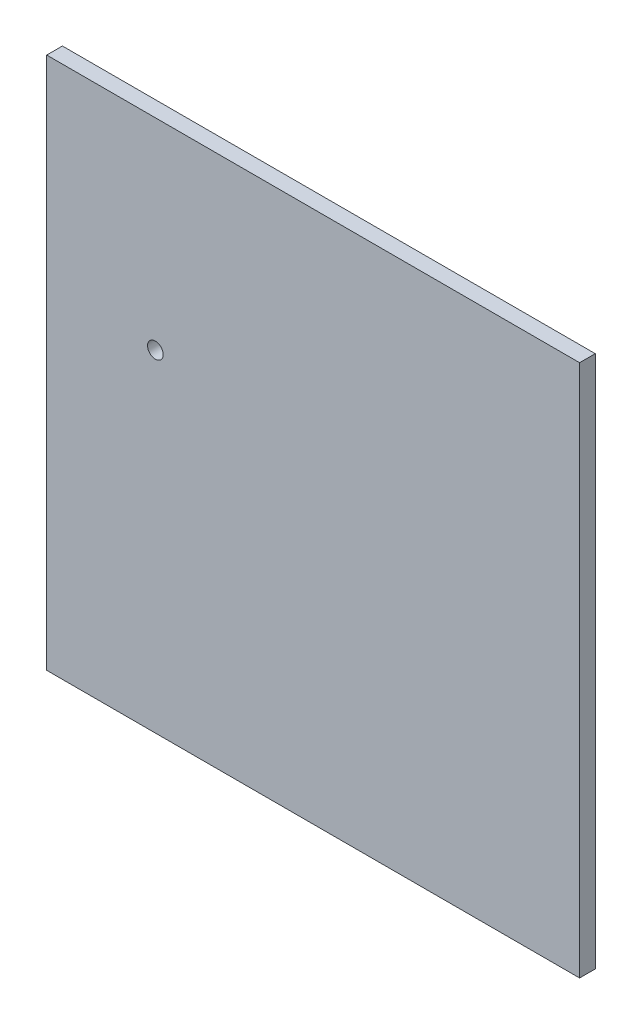
SolidWorks part; units mm, degrees
ref_plane "Plan de face" through (0, 0, 0) normal (1, 0, 0) x (0, 1, 0)
ref_plane "Plan de dessus" through (0, 0, 0) normal (0, 0, 1) x (0, 1, 0)
ref_plane "Plan de droite" through (0, 0, 0) normal (0, 1, 0) x (-1, 0, 0)
sketch "Esquisse3" plane through (0, 0, 0) normal (0, 0, 1) x (0, 1, 0)
  line L1 (-17, -17) -> (17, -17)
  line L2 (-17, -17) -> (-17, 17)
  line L3 (-17, 17) -> (17, 17)
  line L4 (17, -17) -> (17, 17)
  line L5 (-17, -17) -> (17, 17) construction
  line L6 (-17, 17) -> (17, -17) construction
  point P0 (0, 0)
  dimension "D1" = 34
  dimension "D2" = 34
extrude "Boss.-Extru.1" add sketch "Esquisse3" along normal blind 1
sketch "Sketch_Holes" plane through (0, 0, 1) normal (0, 0, 1) x (1, 0, 0)
  circle A0 centre (-10.0677, 4.1602) radius 0.5
extrude "Cut_Extrude_Holes" cut sketch "Sketch_Holes" against normal through all
equation "\"Plaque_L\"=\"Cavite_L\"+\"Cavite_E\"'longueur plaque"
equation "\"Plaque_H\"= \"Cavite_L\"+\"Cavite_E\"'largeur plaque"
equation "\"Plaque_E\"= 2mm'épaisseur plaque superieure et inferieure"
equation "\"Trou_R\"= 1.2mm'rayon perforation base"
equation "\"Trou_dx\"= 4mm'distance entre trou sur x"
equation "\"Trou-dy\"= 4mm'distance entre trou sur y"
equation "\"Cavite_H\"= 18mm'hauteur cavité"
equation "\"Cavite_L\"=\"Cavite_largeur\"+\"Cavite_E\"'longueur cavité"
equation "\"Cavite_E\"= 3mm'épaisseur cavité"
equation "\"Offset_Z\"= 0mm"
equation "\"D1@Esquisse3\"=\"Plaque_H\""
equation "\"D2@Esquisse3\"=\"Plaque_L\""
equation "\"D1@Boss.-Extru.1\"=\"Epaisseur_plaque_perf\""
equation "\"N_Plaque\"= 7"
equation "\"N_Cavite\"= 6"
equation "\"Cavite_largeur\"= 28mm'largeur cavité"
equation "\"Offset_cavite\"= \"Cavite_E\" / 2"
equation "\"Offset_hauteur_vis1\"= \"Cavite_E\""
equation "\"Offset_hauteur_vis2\"= \"Cavite_H\" - \"Cavite_E\""
equation "\"H_total\"=113mm'122-2*2"
equation "\"espace_vis\"=22.6mm'"
equation "\"Largeur_equerre_enveloppe\"=\"Cavite_L\"+\"Cavite_E\""
equation "\"Enveloppe_E\"=5mm"
equation "\"Offset_Enveloppe\"= \"Enveloppe_E\" / 2"
equation "\"Longueur_equerre_enveloppe\"=\"Cavite_L\"+\"Cavite_E\"+\"Enveloppe_E\""
equation "\"largeur_plaque_enveloppe\"=\"Longueur_equerre_enveloppe\"+\"Enveloppe_E\""
equation "\"Epaisseur_plaque_perf\"= 1mm"
